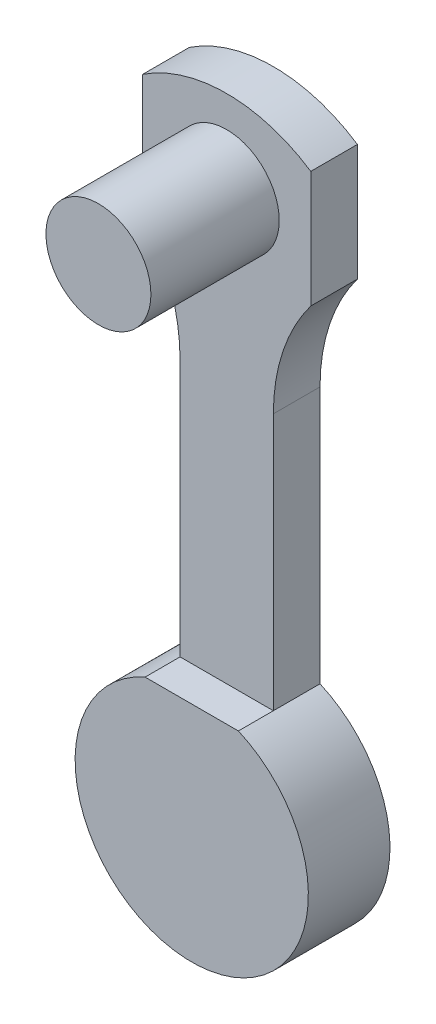
SolidWorks part; units mm, degrees
ref_plane "Piano frontale" through (0, 0, 0) normal (0, 0, 1) x (1, 0, 0)
ref_plane "Piano superiore" through (0, 0, 0) normal (0, 1, 0) x (1, 0, 0)
ref_plane "Piano destro" through (0, 0, 0) normal (1, 0, 0) x (0, 0, -1)
sketch "Schizzo1" plane through (0, 0, 0) normal (0, 0, 1) x (1, 0, 0)
  line L0 (-19.7357, 33.8891) -> (-19.7357, 43.8891)
  line L1 (-5.3236, 43.8891) -> (-5.3236, 33.8891)
  line L2 (-16.5297, 24.281) -> (-16.5297, 2.231)
  line L3 (-8.5297, 24.281) -> (-8.5297, 2.231)
  arc A0 (-19.7357, 43.8891) -> (-5.3236, 43.8891) centre (-12.5297, 33.0691) cw
  arc A1 (-19.7357, 33.8891) -> (-16.5297, 24.281) centre (-32.5297, 24.281) cw
  arc A2 (-5.3236, 33.8891) -> (-8.5297, 24.281) centre (7.4703, 24.281) ccw
  arc A3 (-16.5297, 2.231) -> (-8.5297, 2.231) centre (-12.5297, -6.9342) ccw
  point P16 (-12.5297, 46.0691)
  dimension "D1" = 10
  dimension "D2" = 13
  dimension "D5" = 16
  dimension "D3" = 8
  dimension "D4" = 10
  dimension "D6" = 22.05
extrude "Estrusione-Estrusione1" add sketch "Schizzo1" along normal blind 5 and the other way blind 2
sketch "Schizzo4" plane through (0, 0, 5) normal (0, 0, 1) x (1, 0, 0)
  line L1 (-19.7357, 43.8891) -> (-19.7357, 33.8891) construction
  circle A0 centre (-12.5297, 38.8891) radius 4.5
  arc A1 (-16.5297, 2.231) -> (-8.5297, 2.231) centre (-12.5297, -6.9342) ccw construction
  point P8 (-12.5297, -16.9342)
  point P9 (-19.7357, 38.8891)
  dimension "D1" = 9
extrude "Estrusione-Estrusione3" add sketch "Schizzo4" along normal blind 8
sketch "Schizzo5" plane through (0, 0, -2) normal (0, 0, -1) x (-1, 0, 0)
  line L0 (8.5297, 2.231) -> (8.5297, 24.281) construction
  line L1 (7.5297, -1.9342) -> (17.5297, -1.9342)
  line L2 (7.5297, -1.9342) -> (7.5297, -11.9342)
  line L3 (7.5297, -11.9342) -> (17.5297, -11.9342)
  line L4 (17.5297, -1.9342) -> (17.5297, -11.9342)
  arc A1 (8.5297, 2.231) -> (16.5297, 2.231) centre (12.5297, -6.9342) ccw construction
  point P8 (7.5297, -6.9342)
  point P9 (12.5297, -16.9342)
  point P14 (12.5297, -1.9342)
  dimension "D1" = 10
  dimension "D2" = 10
  dimension "D3" = 4
extrude "Taglio-Estrusione1" cut sketch "Schizzo5" against normal blind 6
sketch "Schizzo6" plane through (-16.5297, 0, 0) normal (-1, 0, 0) x (0, 0, 1)
  line L0 (-2, 2.231) -> (5, 2.231) construction
  line L6 (5, 24.281) -> (5, 2.231) construction
  line L7 (2, 2.231) -> (7.8839, 2.231)
  line L8 (2, 2.231) -> (2, 33.9967)
  line L9 (2, 33.9967) -> (7.8839, 33.9967)
  line L10 (7.8839, 2.231) -> (7.8839, 33.9967)
  dimension "D2" = 3
extrude "Taglio-Estrusione3" cut sketch "Schizzo6" against normal blind 15 and the other way blind 15
sketch "Schizzo7" plane through (0, 0, 5) normal (0, 0, 1) x (1, 0, 0)
  line L0 (-26.3422, 45.2668) -> (-24.6102, 33.4893)
  line L1 (-24.6102, 33.4893) -> (-19.7357, 33.8891)
  line L2 (-19.7357, 33.8891) -> (-1.0553, 33.8891)
  line L3 (-1.0553, 33.8891) -> (-1.9884, 45.2668)
  line L4 (-1.9884, 45.2668) -> (-13.8689, 49.7589)
  line L5 (-13.8689, 49.7589) -> (-26.3422, 45.2668)
  circle A0 centre (-12.5297, 38.8891) radius 4.5
  circle A1 centre (-12.5297, 38.8891) radius 4.5 construction
extrude "Taglio-Estrusione4" cut sketch "Schizzo7" against normal up to surface (3 mm away) up to face at (-12.5297, 23.6645, 2)
